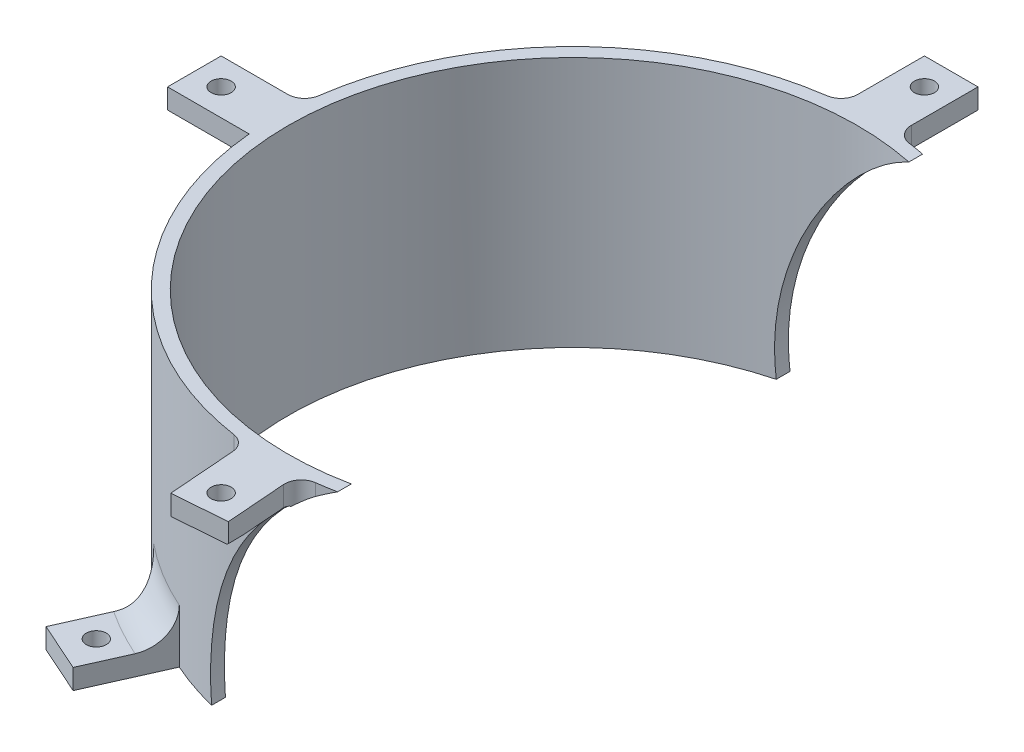
SolidWorks part; units mm, degrees
ref_plane "Front Plane" through (0, 0, 0) normal (0, 0, 1) x (1, 0, 0)
ref_plane "Top Plane" through (0, 0, 0) normal (0, 1, 0) x (1, 0, 0)
ref_plane "Right Plane" through (0, 0, 0) normal (1, 0, 0) x (0, 0, -1)
sketch "Sketch1" plane through (0, 0, 0) normal (0, 1, 0) x (1, 0, 0)
  circle A0 centre (0, 0) radius 85
  circle A1 centre (0, 0) radius 89
  arc A2 (-85, 0) -> (85, 0) centre (0, 0) cw construction
  arc A3 (-89, 0) -> (89, 0) centre (0, 0) cw construction
  dimension "D1" = 85
  dimension "D2" = 4
extrude "Boss-Extrude1" add sketch "Sketch1" along normal blind 75
sketch "Sketch2" plane through (0, 75, 0) normal (0, 1, 0) x (1, 0, 0)
  line L0 (8, 88.6397) -> (8, 113)
  line L1 (8, 113) -> (-8, 113)
  line L2 (-8, 113) -> (-8, 88.6397)
  line L3 (0, 0) -> (0, 105) construction
  line L4 (-113, 8) -> (-88.6397, 8)
  line L5 (-113, 8) -> (-113, -8)
  line L6 (-113, -8) -> (-88.6397, -8)
  line L17 (-88.6397, -8) -> (-85.6239, -8)
  line L18 (-85.6239, -8) -> (-85.6239, 8)
  line L19 (-85.6239, 8) -> (-88.6397, 8)
  line L20 (8, 88.6397) -> (8, 86.3334)
  line L21 (8, 86.3334) -> (-8, 86.3334)
  line L22 (-8, 86.3334) -> (-8, 88.6397)
  line L23 (6.6683, -87.267) -> (8.5101, -111.3701)
  line L24 (8.5101, -111.3701) -> (-7.4434, -112.5892)
  line L25 (-7.4434, -112.5892) -> (-9.3783, -87.267)
  line L26 (-9.3783, -87.267) -> (6.6683, -87.267)
  circle A1 centre (0, 0) radius 105 construction
  circle A2 centre (0, 105) radius 3
  circle A3 centre (-105, 0) radius 3
  circle A5 centre (0, 0) radius 89 construction
  circle A6 centre (0, -105) radius 3
  circle A7 centre (0, 0) radius 89 construction
  dimension "D1" = 210
  dimension "D2" = 6
  dimension "D3" = 6
  dimension "D14" = 6
  dimension "D5" = 8
  dimension "D6" = 8
  dimension "D7" = 8
  dimension "D8" = 8
  dimension "D9" = 8
  dimension "D10" = 8
  dimension "D15" = 8
  dimension "D16" = 8
  dimension "D17" = 7
extrude "Boss-Extrude2" add sketch "Sketch2" against normal blind 6
fillet "Fillet1" radius 5 8 edges at (-89, 69, 0) (-88.6397, 72, -8) (0, 69, -89) (-1.2562, 69, 88.9911) (-8, 72, -88.6397) (8, 72, -88.6397) (6.781, 72, 88.7413) (-9.283, 72, 88.5146)
sketch "Sketch3" plane through (0, 0, 0) normal (0, -1, 0) x (1, 0, 0)
  line L0 (-113, 8) -> (-93.659, 8) construction
  line L1 (-113, -8) -> (-93.659, -8) construction
  line L2 (-113, -8) -> (-113, 8) construction
  line L3 (-113, 8) -> (-88.6397, 8)
  line L4 (-113, -8) -> (-88.6397, -8)
  line L5 (-113, -8) -> (-113, 8)
  line L6 (-88.6397, -8) -> (-86.5768, -8)
  line L7 (-86.5768, -8) -> (-86.5768, 8)
  line L8 (-86.5768, 8) -> (-88.6397, 8)
  line L9 (-45.9612, -103.2306) -> (-35.1057, -78.8488)
  line L10 (-45.9612, -103.2306) -> (-60.578, -96.7229)
  line L11 (-60.578, -96.7229) -> (-49.4614, -71.7547)
  line L12 (-49.4614, -71.7547) -> (-35.1057, -78.8488)
  line L13 (-35.5287, 79.7987) -> (-45.9612, 103.2306)
  line L14 (-45.9612, 103.2306) -> (-60.578, 96.7229)
  line L15 (-60.578, 96.7229) -> (-48.9386, 70.5803)
  line L16 (-48.9386, 70.5803) -> (-35.5287, 79.7987)
  circle A0 centre (0, 0) radius 89 construction
  point P17 (-86.5768, 0)
  dimension "D1" = 16
  dimension "D2" = 113
  dimension "D3" = 66
  dimension "D4" = 113
  dimension "D5" = 16
  dimension "D6" = 132
extrude "Boss-Extrude3" add sketch "Sketch3" against normal blind 6
fillet "Fillet2" radius 10 7 edges at (-88.6397, 3, -8) (-88.6397, 3, 8) (-89, 6, 0) (-43.3901, 6, -77.7065) (-50.2265, 3, -73.4731) (-43.3901, 6, 77.7065) (-50.2265, 3, 73.4731)
sketch "Sketch4" plane through (0, 6, 0) normal (0, 1, 0) x (1, 0, 0)
  line L0 (-53.2696, -99.9767) -> (-45.6622, -82.8901) construction
  line L1 (-45.9612, -103.2306) -> (-60.578, -96.7229) construction
  line L2 (-53.2696, 99.9767) -> (-42.9827, 76.8721) construction
  line L3 (-60.578, 96.7229) -> (-45.9612, 103.2306) construction
  circle A0 centre (-105, 0) radius 3 construction
  circle A1 centre (-105, 0) radius 3
  circle A2 centre (-49.8916, -92.3896) radius 3
  circle A3 centre (-49.8916, 92.3896) radius 3
  dimension "D1" = 6
  dimension "D2" = 6
  dimension "D3" = 105
  dimension "D4" = 105
extrude "Cut-Extrude1" cut sketch "Sketch4" against normal through all
sketch "Sketch5" plane through (0, 0, 0) normal (0, 0, 1) x (1, 0, 0)
  line L0 (89, 0) -> (89, 75) construction
  line L1 (89, 77.4697) -> (165.9577, -10.5357)
  line L2 (165.9577, -10.5357) -> (27.4359, -65.8768)
  line L3 (27.4359, -65.8768) -> (-25.1983, -65.8768)
  line L4 (-25.1983, -65.8768) -> (-21.4886, 0)
  arc A0 (89, 77.4697) -> (-21.4886, 0) centre (55.4082, 7.8538) ccw
extrude "Cut-Extrude2" cut sketch "Sketch5" against normal through all and the other way through all
